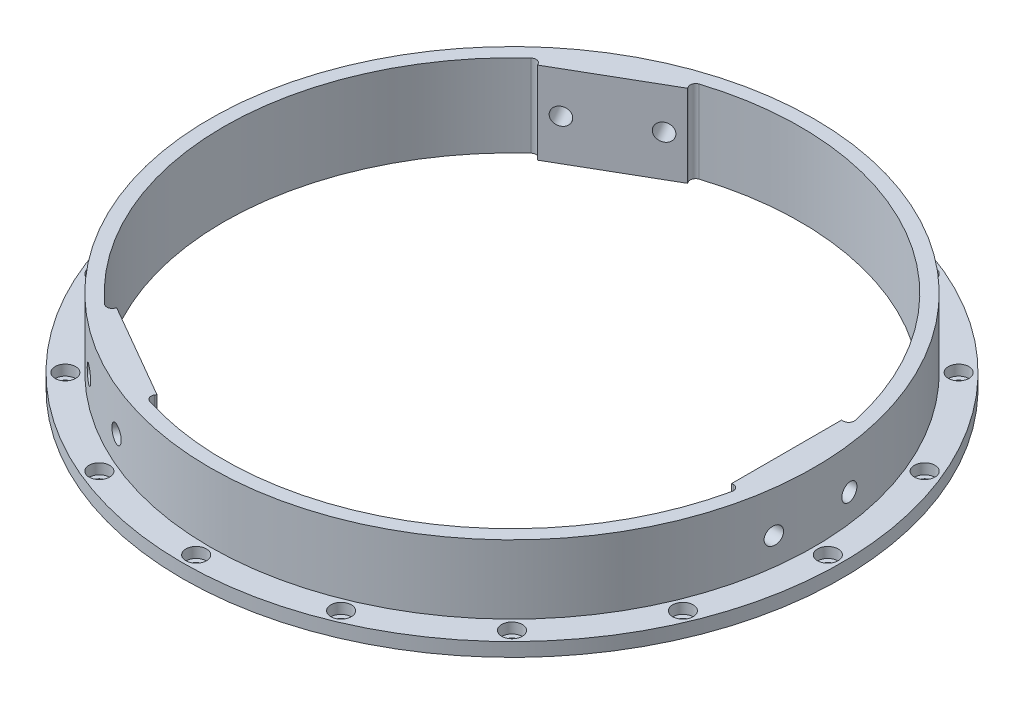
SolidWorks part; units mm, degrees
ref_plane "Front Plane" through (0, 0, 0) normal (0, 0, 1) x (1, 0, 0)
ref_plane "Top Plane" through (0, 0, 0) normal (0, 1, 0) x (1, 0, 0)
ref_plane "Right Plane" through (0, 0, 0) normal (1, 0, 0) x (0, 0, -1)
sketch "Sketch1" plane through (0, 0, 0) normal (0, 1, 0) x (1, 0, 0)
  circle A0 centre (0, 0) radius 152.4
  circle A1 centre (0, 0) radius 133.35
  dimension "D1" = 304.8
  dimension "D2" = 266.7
extrude "Boss-Extrude1" add sketch "Sketch1" along normal blind 38.1
sketch "Sketch2" plane through (0, 38.1, 0) normal (0, 1, 0) x (1, 0, 0)
  circle A0 centre (0, 0) radius 139.7
  circle A1 centre (0, 0) radius 152.4 construction
  circle A2 centre (0, 0) radius 152.4
  dimension "D1" = 279.4
extrude "Cut-Extrude1" cut sketch "Sketch2" against normal blind 31.75
sketch "Sketch3" plane through (0, 38.1, 0) normal (0, 1, 0) x (1, 0, 0)
  line L0 (127, 25.4) -> (127, -25.4)
  line L1 (127, 25.4) -> (130.9086, 25.4)
  line L2 (127, -25.4) -> (130.9086, -25.4)
  circle A0 centre (0, 0) radius 133.35 construction
  arc A1 (130.9086, -25.4) -> (130.9086, 25.4) centre (0, 0) ccw
  point P2 (127, 0)
  dimension "D1" = 50.8
  dimension "D2" = 127
extrude "Boss-Extrude2" add sketch "Sketch3" against normal through all
fillet "Fillet1" radius 2.54 2 edges at (130.9086, 19.05, -25.4) (130.9086, 19.05, 25.4)
hole_wizard "Hole1" positions "Sketch4" profile "Sketch5" legacy
sketch "Sketch4" plane through (127, 0, -417.9439) normal (-1, 0, 0) x (0, 0, 1)
  line L6 (392.5439, 0) -> (443.3439, 0) construction
  line L7 (417.9439, 19.05) -> (417.9439, 0)
  line L8 (400.4814, 19.05) -> (435.4064, 19.05)
  line L10 (435.4064, 19.05) -> (443.3439, 19.05)
  line L11 (443.3439, 0) -> (443.3439, 38.1) construction
  point P0 (400.4814, 19.05)
  point P2 (435.4064, 19.05)
  dimension "D1" = 34.925
sketch "Sketch5" plane through (127, 19.05, -17.4625) normal (0, 1, 0) x (0, 0, 1)
  line L0 (0, 0) -> (0, 81.1823)
  line L1 (0, 81.1823) -> (4, 81.1823)
  line L2 (4, 81.1823) -> (4, 0)
  line L3 (4, 0) -> (0, 0)
  line L4 (0, 110) -> (0, -10) construction
  dimension "Diameter" = 8
  dimension "Depth" = 81.1823
pattern_circular "CirPattern1" count 3 over 360 about axis through (0, 0, 0) along (0, 1, 0) of "Boss-Extrude2", "Fillet1", "Hole1"
hole_wizard "CBORE for #10 Socket Head Cap Screw1" positions "Sketch6" profile "Sketch8" counterbore size "#10" standard "ANSI Inch"
sketch "Sketch6" plane through (0, 6.35, 0) normal (0, 1, 0) x (1, 0, 0)
  line L0 (0, 0) -> (146.05, 0)
  point P0 (146.05, 0)
  dimension "D1" = 146.05
sketch "Sketch8" plane through (146.05, 6.35, 0) normal (1, 0, 0) x (0, 0, 1)
  line L0 (0, 0) -> (0, 9.4078)
  line L1 (0, 9.4078) -> (2.5527, 7.874)
  line L2 (2.5527, 7.874) -> (2.5527, 4.826)
  line L3 (2.5527, 4.826) -> (4.7625, 4.826)
  line L4 (4.7625, 4.826) -> (4.7625, 0)
  line L5 (4.7625, 0) -> (0, 0)
  line L10 (0, 9.4078) -> (-2.5527, 7.874) construction
  line L11 (0, -6.35) -> (0, 107.95) construction
  dimension "Hole Dia." = 5.1054
  dimension "Hole Depth" = 7.874
  dimension "C'Bore Dia." = 9.525
  dimension "C'Bore Depth" = 4.826
  dimension "Drill Angle" = 118
pattern_circular "CirPattern2" count 16 over 360 about axis through (0, 0, 0) along (0, 1, 0) of "CBORE for #10 Socket Head Cap Screw1"
